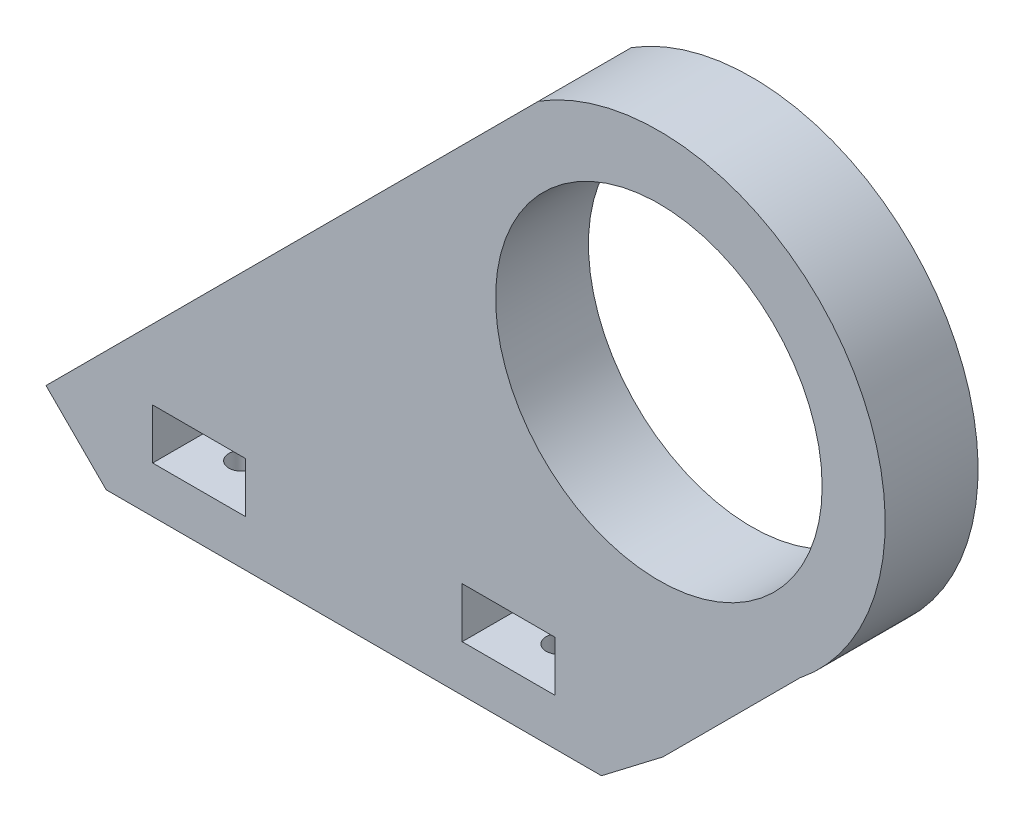
SolidWorks part; units mm, degrees
ref_plane "Front Plane" through (0, 0, 0) normal (0, 0, 1) x (1, 0, 0)
ref_plane "Top Plane" through (0, 0, 0) normal (0, 1, 0) x (1, 0, 0)
ref_plane "Right Plane" through (0, 0, 0) normal (1, 0, 0) x (0, 0, -1)
sketch "Sketch1" plane through (0, 0, 0) normal (0, 0, 1) x (1, 0, 0)
  line L0 (0, 0) -> (64, 0)
  line L1 (0, 0) -> (-7.7782, 7.7782)
  line L2 (-7.7782, 7.7782) -> (55.8614, 71.4178)
  line L3 (64, 0) -> (71.9419, 6.0766)
  line L4 (71.9419, 6.0766) -> (89.6196, 23.7543)
  arc A0 (89.6196, 23.7543) -> (55.8614, 71.4178) centre (71.415, 46.6472) ccw
  dimension "D1" = 64
  dimension "D2" = 90
  dimension "D3" = 11
  dimension "D4" = 10
  dimension "D5" = 25
extrude "Boss-Extrude2" add sketch "Sketch1" along normal blind 12
sketch "Sketch5" plane through (0, 0, 0) normal (0, -1, 0) x (1, 0, 0)
  line L0 (0, 12) -> (0, 0) construction
  line L1 (0, 12) -> (64, 12) construction
  circle A0 centre (11.5, 6) radius 1.65
  circle A1 centre (52.5, 6) radius 1.65
  dimension "D1" = 3.3
  dimension "D2" = 11.5
  dimension "D4" = 6
  dimension "D3" = 2
extrude "Cut-Extrude3" cut sketch "Sketch5" against normal blind 6
sketch "Sketch6" plane through (0, 0, 12) normal (0, 0, 1) x (1, 0, 0)
  line L0 (0, 0) -> (64, 0) construction
  line L1 (18, 12.5) -> (6, 12.5)
  line L2 (18, 12.5) -> (18, 6)
  line L3 (18, 6) -> (6, 6)
  line L4 (6, 12.5) -> (6, 6)
  line L5 (12, 6) -> (12, 12.5) construction
  line L6 (18, 9.25) -> (6, 9.25) construction
  line L7 (58, 12.5) -> (58, 6)
  line L8 (58, 12.5) -> (46, 12.5)
  line L9 (46, 12.5) -> (46, 6)
  line L10 (58, 6) -> (46, 6)
  point P0 (12, 9.25)
  dimension "D1" = 6
  dimension "D2" = 12
  dimension "D3" = 12
  dimension "D4" = 6.5
  dimension "D5" = 2
extrude "Cut-Extrude4" cut sketch "Sketch6" against normal through all
sketch "Sketch8" plane through (0, 0, 0) normal (0, -1, 0) x (1, 0, 0)
  line L4 (0, 0) -> (0, -8)
  line L5 (0, -8) -> (64, -8)
  line L6 (64, -8) -> (64, 0)
  line L7 (64, 0) -> (0, 0)
  dimension "D3" = 8
extrude "Boss-Extrude3" add sketch "Sketch8" against normal blind 5
sketch "Sketch11" plane through (0, 0, 0) normal (0, -1, 0) x (1, 0, 0)
  line L0 (0, 0) -> (0, -8) construction
  circle A0 centre (11.5, -4) radius 1.65
  circle A2 centre (11.5, 6) radius 1.65 construction
  circle A3 centre (52.5, -4) radius 1.65
  dimension "D1" = 3.3
  dimension "D2" = 10
  dimension "D4" = 11.5
  dimension "D3" = 2
extrude "Cut-Extrude7" cut sketch "Sketch11" against normal through all
sketch "Sketch13" plane through (0, 0, 12) normal (0, 0, 1) x (1, 0, 0)
  circle A0 centre (71.415, 46.6472) radius 21.1
  arc A1 (89.6196, 23.7543) -> (55.8614, 71.4178) centre (71.415, 46.6472) ccw construction
  dimension "D1" = 42.2
  dimension "D2" = 0
extrude "Cut-Extrude8" cut sketch "Sketch13" against normal through all
sketch "Sketch15" plane through (0, 5, 0) normal (0, 1, 0) x (1, 0, 0)
  line L0 (0, 8) -> (64, 8) construction
  arc A0 (19, 8) -> (45, 8) centre (32, 21) ccw
  point P0 (19, 8)
  point P1 (32, 8)
  point P4 (45, 8)
  line M6 (64, 8) -> (0, 8)
  dimension "D1" = 13
  dimension "12" = 13
extrude "Cut-Extrude9" cut sketch "Sketch15" against normal blind 10 and the other way through all contours A0 M6
